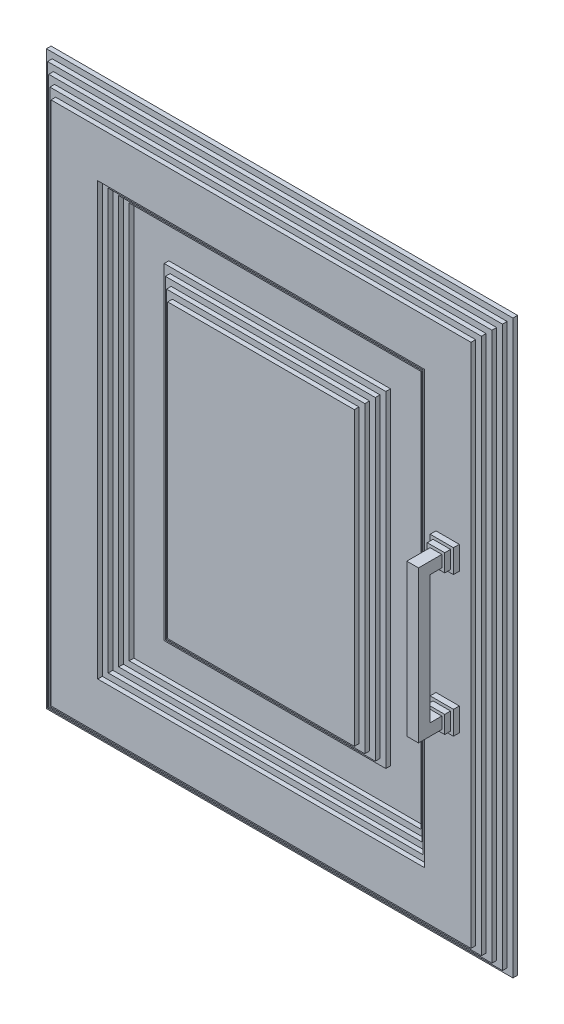
SolidWorks part; units mm, degrees
material "Mahogany"
ref_plane "Front Plane" through (0, 0, 0) normal (0, 0, 1) x (1, 0, 0)
ref_plane "Top Plane" through (0, 0, 0) normal (0, 1, 0) x (1, 0, 0)
ref_plane "Right Plane" through (0, 0, 0) normal (1, 0, 0) x (0, 0, -1)
sketch "Sketch1" plane through (0, 0, 0) normal (0, 0, 1) x (1, 0, 0)
  line L20 (200, 0) -> (200, -20)
  line L21 (200, -20) -> (200, -245)
  line L22 (-200, -245) -> (200, -245)
  line L23 (-200, -20) -> (-200, -245)
  line L24 (-200, 0) -> (-200, -20)
  line L25 (-200, 245) -> (-200, 0)
  line L26 (-200, 245) -> (200, 245)
  line L27 (200, 245) -> (200, 0)
  point P0 (0, 0)
  point P1 (-175, 220)
  point P2 (175, -220)
  point P3 (-175, -220)
  point P4 (175, 220)
extrude "Boss-Extrude2" add sketch "Sketch1" along normal blind 4
sketch "Sketch2" plane through (0, 0, 4) normal (0, 0, 1) x (1, 0, 0)
  line L8 (195, -240) -> (195, 240)
  line L9 (195, 240) -> (-195, 240)
  line L10 (-195, 240) -> (-195, -240)
  line L11 (-195, -240) -> (195, -240)
  line L12 (195, -240) -> (195, 240)
  line L13 (195, 240) -> (-195, 240)
  line L14 (-195, 240) -> (-195, -240)
  line L15 (-195, -240) -> (195, -240)
  dimension "D1" = 5
extrude "Boss-Extrude3" add sketch "Sketch2" along normal blind 4
sketch "Sketch3" plane through (0, 0, 8) normal (0, 0, 1) x (1, 0, 0)
  line L8 (-190, -235) -> (190, -235)
  line L9 (190, -235) -> (190, 235)
  line L10 (190, 235) -> (-190, 235)
  line L11 (-190, 235) -> (-190, -235)
  line L12 (-190, -235) -> (190, -235)
  line L13 (190, -235) -> (190, 235)
  line L14 (190, 235) -> (-190, 235)
  line L15 (-190, 235) -> (-190, -235)
  dimension "D1" = 5
extrude "Boss-Extrude4" add sketch "Sketch3" along normal blind 4
sketch "Sketch4" plane through (0, 0, 12) normal (0, 0, 1) x (1, 0, 0)
  line L8 (-185, 230) -> (-185, -230)
  line L9 (-185, -230) -> (185, -230)
  line L10 (185, -230) -> (185, 230)
  line L11 (185, 230) -> (-185, 230)
  line L12 (-185, 230) -> (-185, -230)
  line L13 (-185, -230) -> (185, -230)
  line L14 (185, -230) -> (185, 230)
  line L15 (185, 230) -> (-185, 230)
  dimension "D1" = 5
extrude "Boss-Extrude5" add sketch "Sketch4" along normal blind 4
sketch "Sketch5" plane through (0, 0, 16) normal (0, 0, 1) x (1, 0, 0)
  line L8 (180, 225) -> (-180, 225)
  line L9 (-180, 225) -> (-180, -225)
  line L10 (-180, -225) -> (180, -225)
  line L11 (180, -225) -> (180, 225)
  line L12 (180, 225) -> (-180, 225)
  line L13 (-180, 225) -> (-180, -225)
  line L14 (-180, -225) -> (180, -225)
  line L15 (180, -225) -> (180, 225)
  dimension "D1" = 5
extrude "Boss-Extrude6" add sketch "Sketch5" along normal blind 4
sketch "Sketch6" plane through (0, 0, 20) normal (0, 0, 1) x (1, 0, 0)
  line L8 (140, -185) -> (140, 185)
  line L9 (140, 185) -> (-140, 185)
  line L10 (-140, 185) -> (-140, -185)
  line L11 (-140, -185) -> (140, -185)
  line L12 (140, -185) -> (140, 185)
  line L13 (140, 185) -> (-140, 185)
  line L14 (-140, 185) -> (-140, -185)
  line L15 (-140, -185) -> (140, -185)
  dimension "D1" = 40
extrude "Cut-Extrude1" cut sketch "Sketch6" against normal blind 4
sketch "Sketch7" plane through (0, 0, 16) normal (0, 0, 1) x (1, 0, 0)
  line L8 (-135, -180) -> (135, -180)
  line L9 (135, -180) -> (135, 180)
  line L10 (135, 180) -> (-135, 180)
  line L11 (-135, 180) -> (-135, -180)
  line L12 (-135, -180) -> (135, -180)
  line L13 (135, -180) -> (135, 180)
  line L14 (135, 180) -> (-135, 180)
  line L15 (-135, 180) -> (-135, -180)
  dimension "D1" = 5
extrude "Cut-Extrude2" cut sketch "Sketch7" against normal blind 4
sketch "Sketch8" plane through (0, 0, 12) normal (0, 0, 1) x (1, 0, 0)
  line L8 (-130, 175) -> (-130, -175)
  line L9 (-130, -175) -> (130, -175)
  line L10 (130, -175) -> (130, 175)
  line L11 (130, 175) -> (-130, 175)
  line L12 (-130, 175) -> (-130, -175)
  line L13 (-130, -175) -> (130, -175)
  line L14 (130, -175) -> (130, 175)
  line L15 (130, 175) -> (-130, 175)
  dimension "D1" = 5
extrude "Cut-Extrude3" cut sketch "Sketch8" against normal blind 4
sketch "Sketch9" plane through (0, 0, 8) normal (0, 0, 1) x (1, 0, 0)
  line L8 (125, 170) -> (-125, 170)
  line L9 (-125, 170) -> (-125, -170)
  line L10 (-125, -170) -> (125, -170)
  line L11 (125, -170) -> (125, 170)
  line L12 (125, 170) -> (-125, 170)
  line L13 (-125, 170) -> (-125, -170)
  line L14 (-125, -170) -> (125, -170)
  line L15 (125, -170) -> (125, 170)
  dimension "D1" = 5
extrude "Cut-Extrude4" cut sketch "Sketch9" against normal blind 4
sketch "Sketch11" plane through (0, 0, 4) normal (0, 0, 1) x (1, 0, 0)
  line L8 (95, -140) -> (95, 140)
  line L9 (95, 140) -> (-95, 140)
  line L10 (-95, 140) -> (-95, -140)
  line L11 (-95, -140) -> (95, -140)
  line L12 (95, -140) -> (95, 140)
  line L13 (95, 140) -> (-95, 140)
  line L14 (-95, 140) -> (-95, -140)
  line L15 (-95, -140) -> (95, -140)
  dimension "D1" = 30
extrude "Boss-Extrude7" add sketch "Sketch11" along normal blind 4
sketch "Sketch12" plane through (0, 0, 8) normal (0, 0, 1) x (1, 0, 0)
  line L8 (-90, -135) -> (90, -135)
  line L9 (90, -135) -> (90, 135)
  line L10 (90, 135) -> (-90, 135)
  line L11 (-90, 135) -> (-90, -135)
  line L12 (-90, -135) -> (90, -135)
  line L13 (90, -135) -> (90, 135)
  line L14 (90, 135) -> (-90, 135)
  line L15 (-90, 135) -> (-90, -135)
  dimension "D1" = 5
extrude "Boss-Extrude8" add sketch "Sketch12" along normal blind 4
sketch "Sketch13" plane through (0, 0, 12) normal (0, 0, 1) x (1, 0, 0)
  line L8 (-85, 130) -> (-85, -130)
  line L9 (-85, -130) -> (85, -130)
  line L10 (85, -130) -> (85, 130)
  line L11 (85, 130) -> (-85, 130)
  line L12 (-85, 130) -> (-85, -130)
  line L13 (-85, -130) -> (85, -130)
  line L14 (85, -130) -> (85, 130)
  line L15 (85, 130) -> (-85, 130)
  dimension "D1" = 5
extrude "Boss-Extrude9" add sketch "Sketch13" along normal blind 4
sketch "Sketch14" plane through (0, 0, 16) normal (0, 0, 1) x (1, 0, 0)
  line L8 (80, 125) -> (-80, 125)
  line L9 (-80, 125) -> (-80, -125)
  line L10 (-80, -125) -> (80, -125)
  line L11 (80, -125) -> (80, 125)
  line L12 (80, 125) -> (-80, 125)
  line L13 (-80, 125) -> (-80, -125)
  line L14 (-80, -125) -> (80, -125)
  line L15 (80, -125) -> (80, 125)
  dimension "D1" = 5
extrude "Boss-Extrude10" add sketch "Sketch14" along normal blind 4
sketch "Sketch15" plane through (0, 0, 20) normal (0, 0, 1) x (1, 0, 0)
  line L0 (-250.7048, 0) -> (237.257, 0) construction
  line L1 (0, 277.7734) -> (0, -276.8061) construction
  line L3 (150, 70) -> (170, 70)
  line L4 (150, 70) -> (150, 50)
  line L5 (150, 50) -> (170, 50)
  line L6 (170, 70) -> (170, 50)
  line L7 (180, -225) -> (180, 225) construction
  line L8 (140, -185) -> (140, 185) construction
  line L9 (150, -50) -> (170, -50)
  line L10 (170, -70) -> (170, -50)
  line L11 (150, -70) -> (170, -70)
  line L12 (150, -70) -> (150, -50)
  dimension "D1" = 50
  dimension "D2" = 20
  dimension "D3" = 20
  dimension "D4" = 10
  dimension "D5" = 10
extrude "Boss-Extrude11" add sketch "Sketch15" along normal blind 5
sketch "Sketch16" plane through (0, 0, 25) normal (0, 0, 1) x (1, 0, 0)
  line L0 (160, 72.9811) -> (160, 48.56) construction
  line L1 (170, 60) -> (150, 60) construction
  line L2 (170, 50) -> (170, 70) construction
  line L3 (150, 70) -> (150, 50) construction
  line L4 (-228.2363, 0) -> (215.6457, 0) construction
  line L5 (167.5, 52.5) -> (152.5, 52.5)
  line L6 (167.5, 52.5) -> (167.5, 67.5)
  line L7 (167.5, 67.5) -> (152.5, 67.5)
  line L8 (152.5, 52.5) -> (152.5, 67.5)
  line L9 (167.5, 52.5) -> (152.5, 67.5) construction
  line L10 (167.5, 67.5) -> (152.5, 52.5) construction
  line L11 (167.5, -67.5) -> (152.5, -67.5)
  line L12 (152.5, -52.5) -> (152.5, -67.5)
  line L13 (167.5, -52.5) -> (152.5, -52.5)
  line L14 (167.5, -52.5) -> (167.5, -67.5)
  point P8 (160, 60)
  dimension "D1" = 15
  dimension "D2" = 15
extrude "Boss-Extrude12" add sketch "Sketch16" along normal blind 5
sketch "Sketch17" plane through (0, 0, 30) normal (0, 0, 1) x (1, 0, 0)
  line L0 (160, 67.5) -> (160, 52.5) construction
  line L1 (167.5, 67.5) -> (152.5, 67.5) construction
  line L2 (152.5, 52.5) -> (167.5, 52.5) construction
  line L3 (152.5, 60) -> (167.5, 60) construction
  line L4 (152.5, 67.5) -> (152.5, 52.5) construction
  line L5 (167.5, 52.5) -> (167.5, 67.5) construction
  line L6 (-224.1377, 0) -> (213.8305, 0) construction
  line L7 (165, 65) -> (155, 65)
  line L8 (165, 65) -> (165, 55)
  line L9 (165, 55) -> (155, 55)
  line L10 (155, 65) -> (155, 55)
  line L11 (165, 65) -> (155, 55) construction
  line L12 (165, 55) -> (155, 65) construction
  line L13 (165, -55) -> (155, -55)
  line L14 (155, -65) -> (155, -55)
  line L15 (165, -65) -> (155, -65)
  line L16 (165, -65) -> (165, -55)
  point P12 (160, 60)
  dimension "D1" = 10
  dimension "D2" = 10
extrude "Boss-Extrude13" add sketch "Sketch17" along normal blind 20
sketch "Sketch18" plane through (0, 55, 0) normal (0, -1, 0) x (1, 0, 0)
  line L0 (165, 50) -> (165, 30) construction
  line L1 (155, 50) -> (165, 50)
  line L2 (155, 50) -> (155, 40)
  line L3 (155, 40) -> (165, 40)
  line L4 (165, 50) -> (165, 40)
extrude "Boss-Extrude14" add sketch "Sketch18" along normal up to next
sketch "Sketch19" plane through (0, 0, 0) normal (0, 0, -1) x (-1, 0, 0)
  line L0 (165, 150) -> (165, 100)
  line L1 (200, 150) -> (200, 100)
  line L2 (200, 150) -> (165, 150)
  line L3 (165, -150) -> (165, -200)
  line L4 (200, -150) -> (200, -200)
  line L5 (200, -150) -> (165, -150)
  line L10 (200, 245) -> (200, -245) construction
  line L13 (200, 100) -> (165, 100)
  line L15 (200, -200) -> (165, -200)
  line L17 (200, -245) -> (-200, -245) construction
  dimension "D3" = 50
  dimension "D2" = 35
  dimension "D4" = 50
  dimension "D5" = 250
  dimension "D6" = 45
  dimension "D14" = 35
extrude "Cut-Extrude5" cut sketch "Sketch19" against normal blind 3
